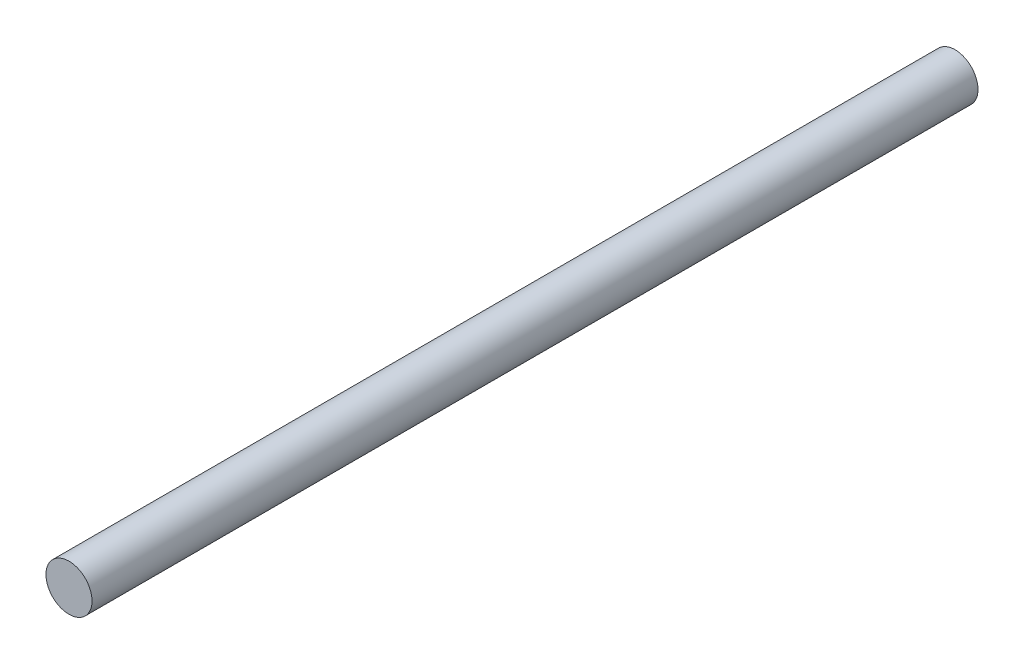
SolidWorks part; units mm, degrees
ref_plane "Plano frontal" through (0, 0, 0) normal (0, 0, 1) x (1, 0, 0)
ref_plane "Plano superior" through (0, 0, 0) normal (0, 1, 0) x (1, 0, 0)
ref_plane "Plano direito" through (0, 0, 0) normal (1, 0, 0) x (0, 0, -1)
sketch "Esboço1" plane through (0, 0, 0) normal (0, 0, 1) x (1, 0, 0)
  circle A0 centre (0, 0) radius 3.9
  dimension "D1" = 7.8
extrude "Ressalto-extrusão1" add sketch "Esboço1" along normal blind 150
